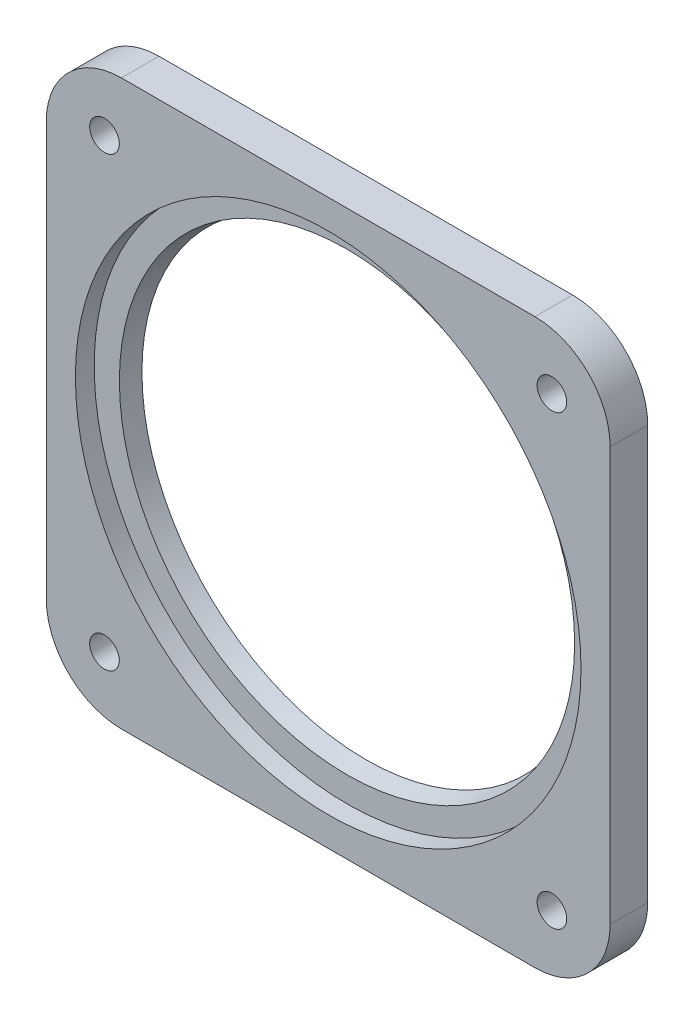
SolidWorks part; units mm, degrees
material "ABS"
ref_plane "Front Plane" through (0, 0, 0) normal (0, 0, 1) x (1, 0, 0)
ref_plane "Top Plane" through (0, 0, 0) normal (0, 1, 0) x (1, 0, 0)
ref_plane "Right Plane" through (0, 0, 0) normal (1, 0, 0) x (0, 0, -1)
sketch "Sketch1" plane through (0, 0, 0) normal (0, 0, 1) x (1, 0, 0)
  line L0 (-95.25, 0) -> (95.25, 0) construction
  line L1 (0, 95.25) -> (0, -95.25) construction
  line L2 (-69.85, 69.85) -> (-87.8105, 87.8105) construction
  line L8 (95.25, 69.85) -> (95.25, -69.85)
  line L9 (69.85, -95.25) -> (-69.85, -95.25)
  line L10 (-95.25, -69.85) -> (-95.25, 69.85)
  line L11 (-69.85, 95.25) -> (69.85, 95.25)
  circle A1 centre (0, 0) radius 89.5985 construction
  circle A2 centre (0, 0) radius 76.8985
  arc A3 (-69.85, -95.25) -> (-95.25, -69.85) centre (-69.85, -69.85) cw
  arc A4 (95.25, -69.85) -> (69.85, -95.25) centre (69.85, -69.85) cw
  arc A5 (95.25, 69.85) -> (69.85, 95.25) centre (69.85, 69.85) ccw
  arc A6 (-95.25, 69.85) -> (-69.85, 95.25) centre (-69.85, 69.85) cw
  point P6 (0, 0)
  point P10 (-78.8303, 78.8303)
  point P15 (0, 0)
  dimension "D2" = 153.797
  dimension "D4" = 12.7
  dimension "D5" = 25.4
  dimension "D3" = 190.5
extrude "Boss-Extrude1" add sketch "Sketch1" along normal blind 12.7
sketch "Sketch4" plane through (0, 0, 0) normal (0, 0, 1) x (1, 0, 0)
  circle A0 centre (0, 0) radius 84.1375 construction
  circle A1 centre (0, 0) radius 76.2
  circle A2 centre (0, 0) radius 85.4075
  dimension "D1" = 152.4
  dimension "D2" = 168.275
  dimension "D3" = 1.27
extrude "Inset Rim" cut sketch "Sketch4" against normal blind 19.05 from offset 25.4
sketch "Sketch6" plane through (0, 0, 0) normal (0, 1, 0) x (1, 0, 0)
  line L3 (-76.8985, 0) -> (-76.8985, -6.35)
  line L5 (0, 10.9982) -> (0, -26.3287) construction
  line L8 (-76.8985, -6.35) -> (-75.6285, 0)
  line L12 (-69.85, 0) -> (-95.25, 0) construction
  line L15 (-75.6285, 0) -> (-76.8985, 0)
  dimension "D1" = 1.27
revolve "Revolve1" add sketch "Sketch6" angle 360 about L5
sketch "Sketch7" plane through (0, 0, 0) normal (0, 0, -1) x (-1, 0, 0)
  line L0 (-87.8105, 87.8105) -> (-63.3557, 63.3557) construction
  line L1 (69.85, 69.85) -> (87.8105, 87.8105) construction
  line L2 (87.8105, -87.8105) -> (63.3557, -63.3557) construction
  line L3 (-87.8105, -87.8105) -> (-63.3557, -63.3557) construction
  arc A0 (-69.85, 95.25) -> (-95.25, 69.85) centre (-69.85, 69.85) ccw construction
  circle A1 centre (0, 0) radius 89.5985 construction
  arc A2 (69.85, -95.25) -> (95.25, -69.85) centre (69.85, -69.85) ccw construction
  arc A3 (-95.25, -69.85) -> (-69.85, -95.25) centre (-69.85, -69.85) ccw construction
  point P10 (-75.5831, 75.5831)
  point P12 (75.5831, 75.5831)
  point P24 (-75.5831, -75.5831)
  point P29 (75.5831, -75.5831)
hole_wizard "CBORE for M8 Hex Head Bolt1" positions "Sketch7" profile "Sketch8" counterbore size "M8" standard "ISO" end condition through all
sketch "Sketch8" plane through (-75.5831, -75.5831, 0) normal (1, 0, 0) x (0, 1, 0)
  line L0 (0, 0) -> (0, 12.7)
  line L1 (0, 12.7) -> (5, 12.7)
  line L3 (5, 12.7) -> (5, 5.3)
  line L4 (5, 5.3) -> (9.0055, 5.3)
  line L5 (9.0055, 5.3) -> (9.0055, 0)
  line L7 (9.0055, 0) -> (0, 0)
  line L11 (0, -6.35) -> (0, 107.95) construction
  dimension "Thru Hole Dia." = 10
  dimension "Thru Hole Depth" = 12.7
  dimension "C'Bore Dia." = 18.011
  dimension "C'Bore Depth" = 5.3
